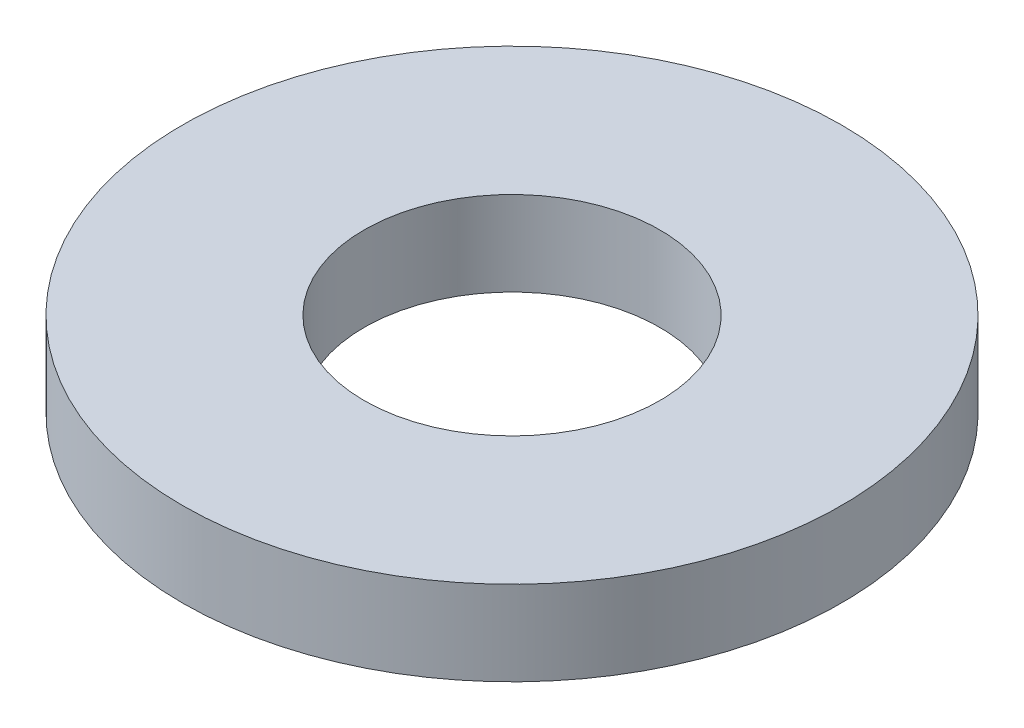
SolidWorks part; units mm, degrees
ref_plane "Front Plane" through (0, 0, 0) normal (0, 0, 1) x (1, 0, 0)
ref_plane "Top Plane" through (0, 0, 0) normal (0, 1, 0) x (1, 0, 0)
ref_plane "Right Plane" through (0, 0, 0) normal (1, 0, 0) x (0, 0, -1)
sketch "Sketch1" plane through (0, 0, 0) normal (0, 1, 0) x (1, 0, 0)
  circle A0 centre (0, 0) radius 3.9624
  dimension "OD" = 7.9248
extrude "Boss-Extrude1" add sketch "Sketch1" along normal blind 1.016
sketch "Sketch5" plane through (0, 1.016, 0) normal (0, 1, 0) x (-1, 0, 0)
  circle A0 centre (0, 0) radius 1.778
  dimension "ID" = 3.556
extrude "Cut-Extrude1" cut sketch "Sketch5" against normal through all
